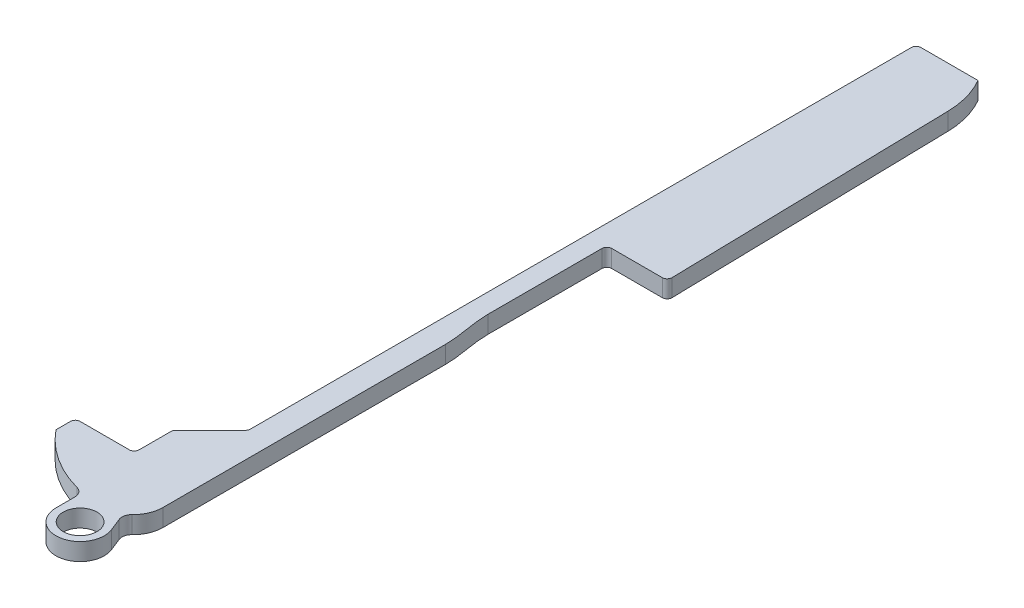
SolidWorks part; units mm, degrees
ref_plane "Front Plane" through (0, 0, 0) normal (0, 0, 1) x (1, 0, 0)
ref_plane "Top Plane" through (0, 0, 0) normal (0, 1, 0) x (1, 0, 0)
ref_plane "Right Plane" through (0, 0, 0) normal (1, 0, 0) x (0, 0, -1)
sketch "Sketch1" plane through (0, 0, 0) normal (0, 1, 0) x (1, 0, 0)
  line L0 (0, 4.5) -> (0, 6.5)
  line L1 (0, 0) -> (18.25, 0) construction
  line L2 (0, 0) -> (0, 83.5) construction
  line L3 (0, 83.5) -> (18.25, 83.5) construction
  line L4 (18.25, 0) -> (18.25, 83.5) construction
  line L5 (0, 6.5) -> (6.1, 6.5)
  line L6 (6.1, 6.5) -> (6.1, 10.5)
  line L7 (6.1, 10.5) -> (10, 14.4)
  line L8 (10, 14.4) -> (10, 83.5)
  line L9 (17.602, 79.1992) -> (18.25, 49.5)
  line L10 (18.25, 49.5) -> (12, 49.5)
  line L11 (12, 37.18) -> (12, 49.5)
  line L12 (12.5, 32.33) -> (12.5, 3.07)
  line L13 (10, 83.5) -> (16.4, 83.5)
  line L14 (12, 39.12) -> (12, 35.2194) construction
  line L15 (12.5, 33.6165) -> (12.5, 30.9888) construction
  arc A0 (17.602, 79.1992) -> (16.4, 83.5) centre (8.6041, 79.0029) ccw
  arc A1 (12.5, 3.07) -> (9.43, 0) centre (9.43, 3.07) cw
  arc A2 (9.43, 0) -> (0, 4.5) centre (9.43, 12.1305) cw
  spline S0 degree 3 poles (12.5, 32.33) (12.5, 33.9723) (12, 35.5548) (12, 37.18) knots 0 0 0 0 1 1 1 1
  point P5 (16.4, 83.5)
  point P6 (0, 4.5)
  point P7 (0, 6.5)
  point P8 (18.25, 49.5)
  dimension "D11" = 3.9
  dimension "D12" = 9
  dimension "D1" = 83.5
  dimension "D2" = 18.25
  dimension "D3" = 1.85
  dimension "D4" = 34
  dimension "D5" = 4.5
  dimension "D6" = 2
  dimension "D7" = 6.1
  dimension "D8" = 4
  dimension "D9" = 45
  dimension "D10" = 1.25
  dimension "D13" = 6.25
  dimension "D14" = 12.32
  dimension "D15" = 4.85
  dimension "D16" = 29.26
  dimension "D17" = 2.5
extrude "Boss-Extrude1" add sketch "Sketch1" along normal blind 1.8
fillet "Fillet2" radius 0.5 7 edges at (12, 0.9, -49.5) (18.25, 0.9, -49.5) (10, 0.9, -14.4) (6.1, 0.9, -10.5) (6.1, 0.9, -6.5) (10, 0.9, -83.5) (0, 0.9, -6.5)
sketch "Sketch3" plane through (0, 0, 0) normal (0, -1, 0) x (1, 0, 0)
  line L0 (12.5, -3.07) -> (12.5, -32.33) construction
  line L1 (7, 2.4998) -> (7, -0.5002)
  line L2 (7, -0.5002) -> (11, -0.5002)
  line L3 (11, -0.5002) -> (11.824, 1.5785)
  circle A0 centre (9.5, 2.4998) radius 2.5
  arc A1 (9.43, 0) -> (0, -4.5) centre (9.43, -12.1305) ccw construction
  circle A2 centre (9.5, 2.4998) radius 1.75
  arc M8 (12.5, -3.07) -> (9.43, 0) centre (9.43, -3.07) ccw
  arc M9 (9.43, 0) -> (0, -4.5) centre (9.43, -12.1305) ccw
  dimension "D1" = 5
  dimension "D5" = 3.5
  dimension "D2" = 3
  dimension "D3" = 3
  dimension "D4" = 4
extrude "Boss-Extrude2" add sketch "Sketch3" against normal blind 1.8 contours A0 A2 | A0 L1 L3 M9 M8 | L2 L3 L1 M8 M9
fillet "Fillet3" radius 1 2 edges at (7, 0.9, -0.2459) (11.0219, 0.9, -0.445)
